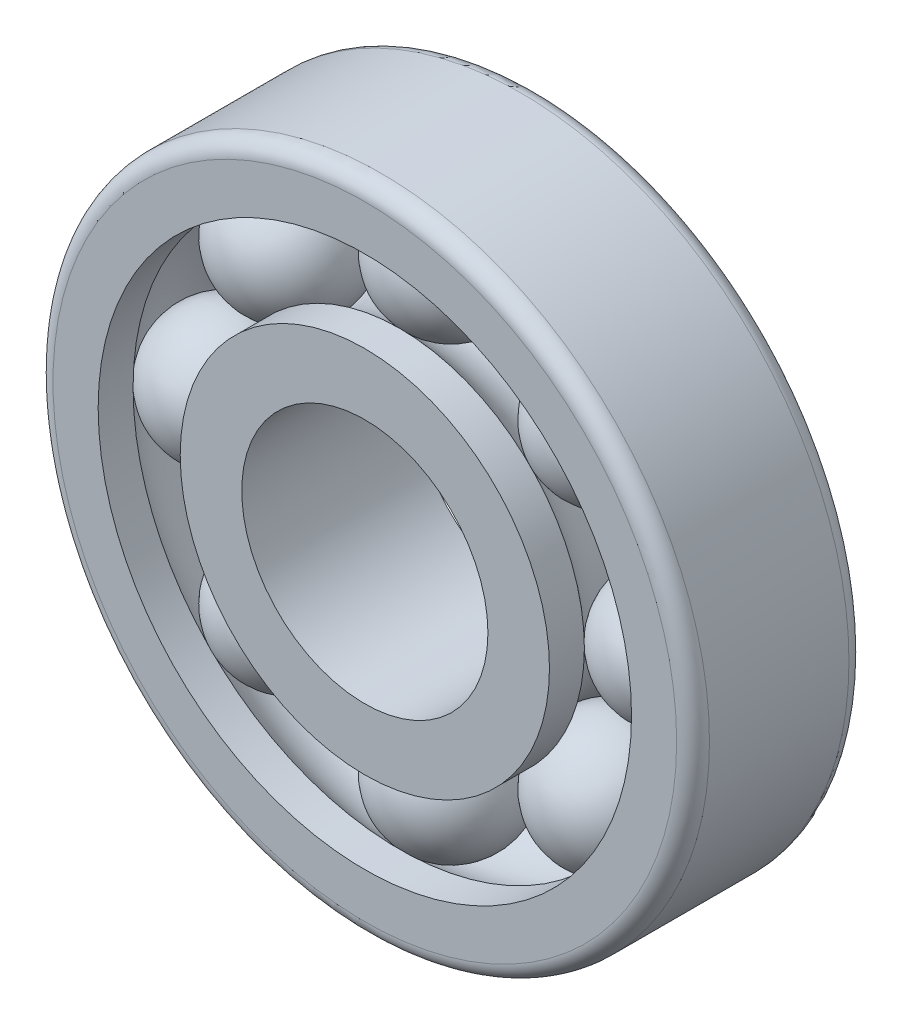
SolidWorks part; units mm, degrees
ref_plane "Front Plane" through (0, 0, 0) normal (0, 0, 1) x (1, 0, 0)
ref_plane "Top Plane" through (0, 0, 0) normal (0, 1, 0) x (1, 0, 0)
ref_plane "Right Plane" through (0, 0, 0) normal (1, 0, 0) x (0, 0, -1)
sketch "Sketch1" plane through (0, 0, 0) normal (0, 0, 1) x (1, 0, 0)
  circle A0 centre (0, 0) radius 15
  circle A1 centre (0, 0) radius 22.5
  circle A2 centre (0, 0) radius 32.5
  circle A3 centre (0, 0) radius 40
  dimension "D1" = 80
  dimension "D2" = 65
  dimension "D3" = 45
  dimension "D4" = 30
extrude "Boss-Extrude1" add sketch "Sketch1" along normal blind 21 contours A3 A2 | A1 A0
sketch "Sketch2" plane through (0, 0, 0) normal (0, 1, 0) x (1, 0, 0)
  line L0 (22.5, -10.5) -> (32.5, -10.5) construction
  line L1 (22.5, -21) -> (22.5, 0) construction
  line L2 (32.5, -21) -> (32.5, 0) construction
  line L3 (0, 0) -> (0, 21.9554) construction
  circle A0 centre (27.5, -10.5) radius 8
  dimension "D1" = 16
revolve "Cut-Revolve1" cut sketch "Sketch2" angle 360 about L3
sketch "Sketch3" plane through (0, 0, 0) normal (0, 1, 0) x (1, 0, 0)
  line L0 (27.5, -2.5) -> (27.5, -18.5)
  arc A0 (27.5, -18.5) -> (27.5, -2.5) centre (27.5, -10.5) ccw
  dimension "D1" = 16
revolve "Revolve1" add sketch "Sketch3" angle 360 about L0
pattern_circular "CirPattern1" count 8 over 360 about axis through (0, 0, 0) along (0, 0, 1) of bodies 105
fillet "Fillet1" radius 2 2 edges at (40, 0, 21) (40, 0, 0)
